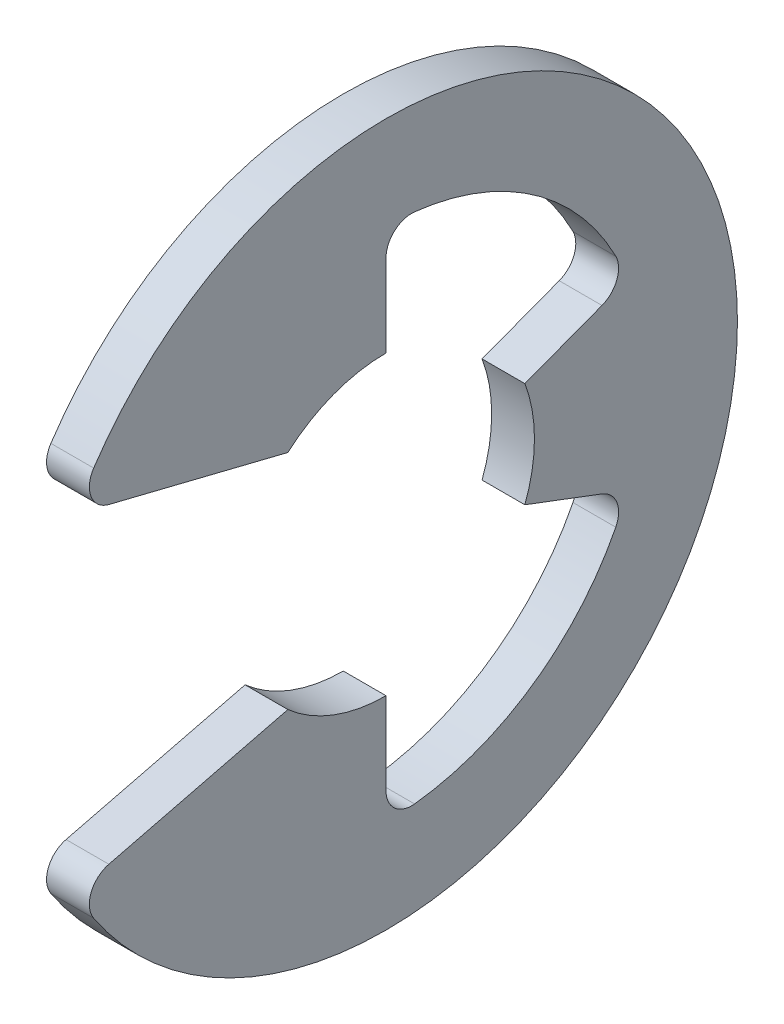
SolidWorks part; units mm, degrees
ref_plane "Front" through (0, 0, 0) normal (0, 0, 1) x (1, 0, 0)
ref_plane "Top" through (0, 0, 0) normal (0, 1, 0) x (1, 0, 0)
ref_plane "Right" through (0, 0, 0) normal (1, 0, 0) x (0, 0, -1)
sketch "Sketch1" plane through (0, 0, 0) normal (1, 0, 0) x (0, 0, -1)
  line L0 (-8.7103, -4.5993) -> (-2.7516, -3.12)
  line L1 (-8.7103, 4.5993) -> (-2.7516, 3.12)
  line L2 (0, -4.16) -> (0, -7.231)
  line L3 (0, 4.16) -> (0, 7.231)
  line L4 (3.8913, -1.4708) -> (6.764, -2.5565)
  line L5 (3.8913, 1.4708) -> (6.764, 2.5565)
  line L6 (0, 0) -> (-10.2, 0) construction
  line L7 (3.8913, 1.4708) -> (3.8913, -1.4708) construction
  line L8 (0, -4.16) -> (-2.7516, -3.12) construction
  circle A1 centre (0, 0) radius 10.2 construction
  circle A2 centre (0, 0) radius 4.16 construction
  arc A3 (-8.7103, -4.5993) -> (-8.7103, 4.5993) centre (0, 0) ccw
  arc A4 (-2.7516, -3.12) -> (0, -4.16) centre (0, 0) ccw
  arc A5 (-2.7516, 3.12) -> (0, 4.16) centre (0, 0) cw
  arc A6 (3.8913, 1.4708) -> (3.8913, -1.4708) centre (0, 0) cw
  arc A7 (0, -7.231) -> (6.764, -2.5565) centre (0, 0) ccw
  arc A8 (6.764, 2.5565) -> (0, 7.231) centre (0, 0) ccw
  dimension "D" = 8.32
  dimension "D1" = 7.231
  dimension "OD" = 19.7
  dimension "D2" = 4.7301
  dimension "D3" = 6.24
extrude "Extrude1" add sketch "Sketch1" along normal mid plane 1.2
fillet "Fillet1" radius 0.72 6 edges at (0, -7.231, 0) (0, 7.231, 0) (0, -4.5993, 8.7103) (0, 4.5993, 8.7103) (0, -2.5565, -6.764) (0, 2.5565, -6.764)
sketch "Sketch3" plane through (0, 0, 0) normal (0, 1, 0) x (1, 0, 0)
  line L0 (0.625, 5.5) -> (0.625, 5)
  line L1 (0.625, 5) -> (-0.625, 5)
  line L2 (-0.625, 5) -> (-0.625, 5.5)
  line L3 (-0.625, 5.5) -> (-8.75, 5.5)
  line L4 (3.75, 0) -> (3.75, 5.25)
  line L5 (-8.75, 5.5) -> (-8.75, 0)
  line L6 (-8.75, 0) -> (3.75, 0)
  line L8 (3.75, 0) -> (3.75, 5.5) construction
  line L9 (3.75, 5.5) -> (0.625, 5.5) construction
  line L10 (3.75, 0) -> (17.2631, 0) construction
  line L11 (3.75, 5.25) -> (3.5, 5.5)
  line L12 (3.5, 5.5) -> (0.625, 5.5)
  point P2 (0, 5)
  point P5 (0.625, 5.25)
  dimension "D2" = 12.5
  dimension "D1" = 3.125
  dimension "D3" = 45
revolve "Revolve2" [suppressed] add sketch "Sketch3" angle 360 about L10
equation "\"D2@Sketch3\" = \"W@Sketch3\"*10"
equation "\"D1@Sketch3\" = \"D2@Sketch3\"/4"
equation "\"D1@Sketch1\" = (\"OD@Sketch1\"+\"D@Sketch1\")/3.875"
equation "\"D3@Sketch1\" = \"D@Sketch1\"*.75"
equation "\"D1@Fillet1\" = \"D1@Extrude1\"*.6"
